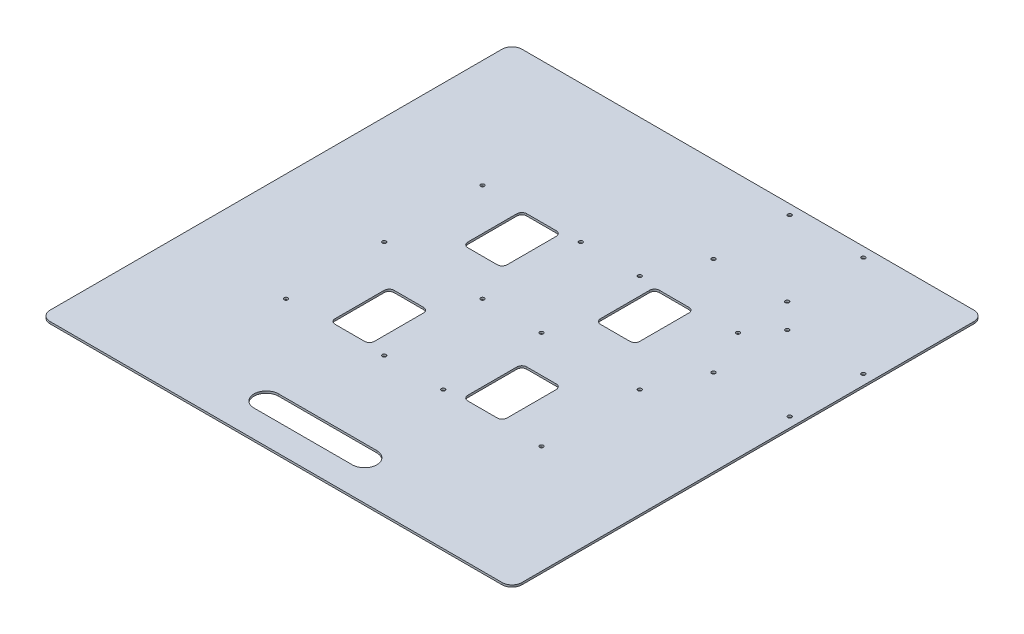
SolidWorks part; units mm, degrees
material "Plain Carbon Steel"
ref_plane "Front Plane" through (0, 0, 0) normal (0, 0, 1) x (1, 0, 0)
ref_plane "Top Plane" through (0, 0, 0) normal (0, 1, 0) x (1, 0, 0)
ref_plane "Right Plane" through (0, 0, 0) normal (1, 0, 0) x (0, 0, -1)
sketch "Sketch1" plane through (0, 0, 0) normal (0, 1, 0) x (1, 0, 0)
  line L1 (-304.8, -304.8) -> (304.8, -304.8)
  line L2 (-304.8, -304.8) -> (-304.8, 304.8)
  line L3 (-304.8, 304.8) -> (304.8, 304.8)
  line L4 (304.8, -304.8) -> (304.8, 304.8)
  line L5 (-304.8, -304.8) -> (304.8, 304.8) construction
  line L6 (-304.8, 304.8) -> (304.8, -304.8) construction
  point P0 (0, 0)
  dimension "D1" = 609.6
  dimension "D2" = 609.6
extrude "Boss-Extrude1" add sketch "Sketch1" along normal blind 2.6568
sketch "Sketch2" plane through (0, 2.6568, 0) normal (0, 1, 0) x (1, 0, 0)
  line L1 (-104.775, 123.825) -> (-66.675, 123.825)
  line L2 (-111.125, 117.475) -> (-111.125, 53.975)
  line L3 (-104.775, 47.625) -> (-66.675, 47.625)
  line L4 (-60.325, 117.475) -> (-60.325, 53.975)
  line L5 (-111.125, 123.825) -> (-60.325, 47.625) construction
  line L6 (-111.125, 47.625) -> (-60.325, 123.825) construction
  line L7 (-104.775, -47.625) -> (-66.675, -47.625)
  line L8 (-111.125, -53.975) -> (-111.125, -117.475)
  line L9 (-104.775, -123.825) -> (-66.675, -123.825)
  line L10 (-60.325, -53.975) -> (-60.325, -117.475)
  line L11 (-111.125, -47.625) -> (-60.325, -123.825) construction
  line L12 (-111.125, -123.825) -> (-60.325, -47.625) construction
  line L13 (66.675, -47.625) -> (104.775, -47.625)
  line L14 (60.325, -53.975) -> (60.325, -117.475)
  line L15 (66.675, -123.825) -> (104.775, -123.825)
  line L16 (111.125, -53.975) -> (111.125, -117.475)
  line L17 (60.325, -47.625) -> (111.125, -123.825) construction
  line L18 (60.325, -123.825) -> (111.125, -47.625) construction
  line L19 (104.775, 123.825) -> (66.675, 123.825)
  line L20 (111.125, 117.475) -> (111.125, 53.975)
  line L21 (104.775, 47.625) -> (66.675, 47.625)
  line L22 (60.325, 117.475) -> (60.325, 53.975)
  line L23 (111.125, 123.825) -> (60.325, 47.625) construction
  line L24 (111.125, 47.625) -> (60.325, 123.825) construction
  arc A0 (66.675, 47.625) -> (60.325, 53.975) centre (66.675, 53.975) cw
  arc A1 (66.675, 123.825) -> (60.325, 117.475) centre (66.675, 117.475) ccw
  arc A2 (-60.325, 117.475) -> (-66.675, 123.825) centre (-66.675, 117.475) ccw
  arc A3 (-60.325, 53.975) -> (-66.675, 47.625) centre (-66.675, 53.975) cw
  arc A4 (-104.775, 47.625) -> (-111.125, 53.975) centre (-104.775, 53.975) cw
  arc A5 (-111.125, 117.475) -> (-104.775, 123.825) centre (-104.775, 117.475) cw
  arc A6 (111.125, 117.475) -> (104.775, 123.825) centre (104.775, 117.475) ccw
  arc A7 (111.125, 53.975) -> (104.775, 47.625) centre (104.775, 53.975) cw
  arc A8 (104.775, -47.625) -> (111.125, -53.975) centre (104.775, -53.975) cw
  arc A9 (111.125, -117.475) -> (104.775, -123.825) centre (104.775, -117.475) cw
  arc A10 (66.675, -123.825) -> (60.325, -117.475) centre (66.675, -117.475) cw
  arc A11 (66.675, -47.625) -> (60.325, -53.975) centre (66.675, -53.975) ccw
  arc A12 (-60.325, -53.975) -> (-66.675, -47.625) centre (-66.675, -53.975) ccw
  arc A13 (-60.325, -117.475) -> (-66.675, -123.825) centre (-66.675, -117.475) cw
  arc A14 (-104.775, -123.825) -> (-111.125, -117.475) centre (-104.775, -117.475) cw
  arc A15 (-104.775, -47.625) -> (-111.125, -53.975) centre (-104.775, -53.975) ccw
  point P0 (-85.725, 85.725)
  point P5 (-85.725, -85.725)
  point P10 (85.725, -85.725)
  point P15 (85.725, 85.725)
  dimension "D7" = 6.35
  dimension "D8" = 6.35
  dimension "D9" = 6.35
  dimension "D1" = 85.725
  dimension "D2" = 85.725
  dimension "D3" = 85.725
  dimension "D4" = 85.725
  dimension "D5" = 76.2
  dimension "D6" = 50.8
extrude "Cut-Extrude1" cut sketch "Sketch2" against normal through all
sketch "Sketch3" plane through (0, 2.6568, 0) normal (0, 1, 0) x (1, 0, 0)
  circle A0 centre (-165.1, 127) radius 2.3876
  circle A1 centre (-165.1, 0) radius 2.3876
  circle A2 centre (-165.1, -127) radius 2.3876
  circle A3 centre (-38.1, 127) radius 2.3876
  circle A4 centre (-38.1, 0) radius 2.3876
  circle A5 centre (-38.1, -127) radius 2.3876
  dimension "D1" = 165.1
  dimension "D5" = 4.7752
  dimension "D2" = 127
  dimension "D3" = 127
  dimension "D4" = 127
extrude "Cut-Extrude2" cut sketch "Sketch3" against normal through all
pattern_linear "LPattern1" count 2 spacing 203.2 of "Cut-Extrude2"
sketch "Sketch4" plane through (0, 2.6568, 0) normal (0, 1, 0) x (1, 0, 0)
  line L0 (-63.5, -254) -> (63.5, -254) construction
  line L1 (-63.5, -238.125) -> (63.5, -238.125)
  line L2 (-63.5, -269.875) -> (63.5, -269.875)
  line L3 (-304.8, -304.8) -> (304.8, -304.8) construction
  arc A0 (-63.5, -238.125) -> (-63.5, -269.875) centre (-63.5, -254) ccw
  arc A1 (63.5, -269.875) -> (63.5, -238.125) centre (63.5, -254) ccw
  point P2 (0, -254)
  dimension "D1" = 31.75
  dimension "D2" = 127
  dimension "D3" = 50.8
extrude "Cut-Extrude3" cut sketch "Sketch4" against normal through all
fillet "Fillet1" radius 12.7
sketch "Sketch5" plane through (0, 2.6568, 0) normal (0, 1, 0) x (1, 0, 0)
  line L0 (304.8, -292.1) -> (304.8, 292.1) construction
  line L1 (66.675, 292.1) -> (161.925, 292.1) construction
  line L2 (66.675, 292.1) -> (66.675, 193.675) construction
  line L3 (66.675, 193.675) -> (161.925, 193.675) construction
  line L4 (161.925, 292.1) -> (161.925, 193.675) construction
  line L5 (66.675, 292.1) -> (161.925, 193.675) construction
  line L6 (66.675, 193.675) -> (161.925, 292.1) construction
  line L7 (292.1, 66.675) -> (193.675, 66.675) construction
  line L8 (292.1, 66.675) -> (292.1, 161.925) construction
  line L9 (292.1, 161.925) -> (193.675, 161.925) construction
  line L10 (193.675, 66.675) -> (193.675, 161.925) construction
  line L11 (292.1, 66.675) -> (193.675, 161.925) construction
  line L12 (292.1, 161.925) -> (193.675, 66.675) construction
  line L13 (292.1, 304.8) -> (-292.1, 304.8) construction
  circle A8 centre (161.925, 292.1) radius 2.3876
  circle A9 centre (66.675, 292.1) radius 2.3876
  circle A10 centre (161.925, 193.675) radius 2.3876
  circle A11 centre (66.675, 193.675) radius 2.3876
  circle A12 centre (193.675, 161.925) radius 2.3876
  circle A13 centre (193.675, 66.675) radius 2.3876
  circle A14 centre (292.1, 66.675) radius 2.3876
  circle A15 centre (292.1, 161.925) radius 2.3876
  point P0 (114.3, 242.8875)
  point P5 (242.8875, 114.3)
  dimension "D1" = 4.7752
  dimension "D2" = 114.3
  dimension "D3" = 114.3
  dimension "D4" = 12.7
  dimension "D5" = 12.7
  dimension "D6" = 98.425
  dimension "D7" = 95.25
extrude "Cut-Extrude4" cut sketch "Sketch5" against normal through all
sketch "Sketch6" plane through (0, 2.6568, 0) normal (0, 1, 0) x (1, 0, 0)
  point P0 (-165.1, 127)
  point P1 (-38.1, 127)
  point P3 (38.1, 127)
  point P5 (66.675, 193.675)
  point P7 (66.675, 292.1)
  point P9 (161.925, 292.1)
  point P11 (161.925, 193.675)
  point P13 (193.675, 161.925)
  point P15 (165.1, 127)
  point P17 (292.1, 161.925)
  point P19 (193.675, 66.675)
  point P21 (292.1, 66.675)
  point P23 (-165.1, 0)
  point P25 (-38.1, 0)
  point P27 (38.1, 0)
  point P29 (165.1, 0)
  point P31 (165.1, -127)
  point P32 (38.1, -127)
  point P33 (-38.1, -127)
  point P37 (-165.1, -127)
hole_wizard "#10 (0.1935) Diameter Hole1" positions "Sketch7" profile "Sketch8" hole size "#10" standard "ANSI Inch" end condition up to next
sketch "Sketch7" plane through (0, 2.6568, 0) normal (0, 1, 0) x (1, 0, 0)
  point P5 (161.925, 292.1)
  point P7 (66.675, 292.1)
  point P9 (292.1, 161.925)
  point P11 (193.675, 161.925)
  point P13 (161.925, 193.675)
  point P15 (66.675, 193.675)
  point P17 (165.1, 127)
  point P19 (38.1, 127)
  point P21 (-38.1, 127)
  point P23 (292.1, 66.675)
  point P25 (193.675, 66.675)
  point P27 (165.1, 0)
  point P29 (165.1, -127)
  point P31 (-38.1, 0)
  point P33 (38.1, 0)
  point P35 (38.1, -127)
  point P37 (-38.1, -127)
  point P39 (-165.1, -127)
  point P41 (-165.1, 0)
  point P43 (-165.1, 127)
sketch "Sketch8" plane through (161.925, 2.6568, -292.1) normal (1, 0, 0) x (0, 0, 1)
  line L0 (0, 0) -> (0, 2.6568)
  line L1 (0, 2.6568) -> (2.4574, 2.6568)
  line L2 (2.4574, 2.6568) -> (2.4574, 0)
  line L5 (2.4574, 0) -> (0, 0)
  line L11 (0, -6.35) -> (0, 107.95) construction
  dimension "Thru Hole Dia." = 4.9149
  dimension "Thru Hole Depth" = 2.6568
